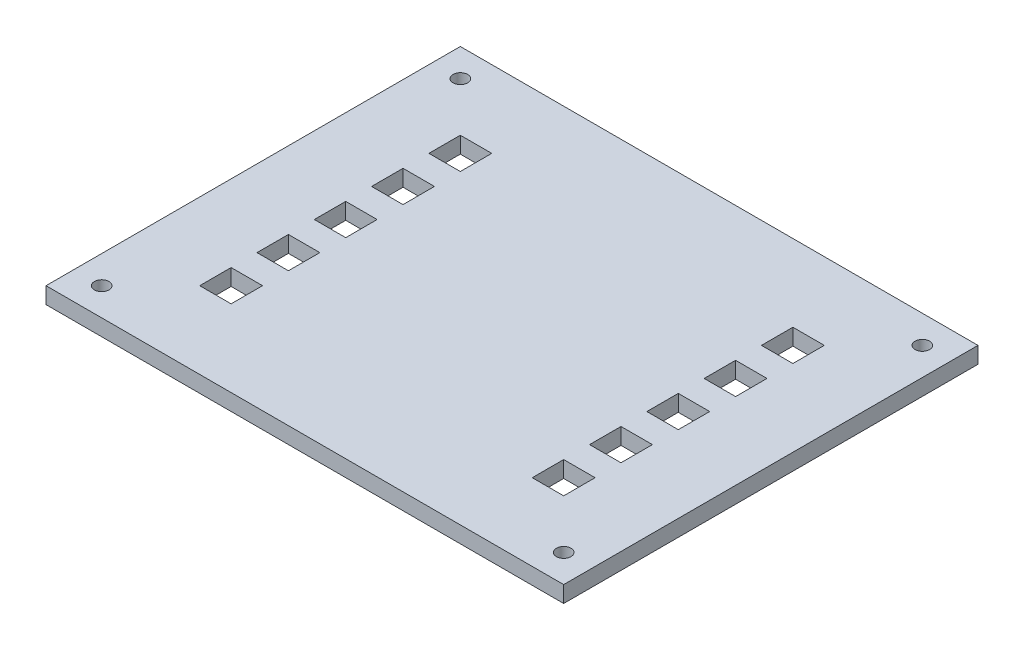
SolidWorks part; units mm, degrees
material "Maple"
ref_plane "Front Plane" through (0, 0, 0) normal (0, 0, 1) x (1, 0, 0)
ref_plane "Top Plane" through (0, 0, 0) normal (0, 1, 0) x (1, 0, 0)
ref_plane "Right Plane" through (0, 0, 0) normal (1, 0, 0) x (0, 0, -1)
sketch "Sketch1" plane through (0, 0, 0) normal (0, 1, 0) x (1, 0, 0)
  line L1 (-50.085, 40.085) -> (50.085, 40.085)
  line L2 (-50.085, 40.085) -> (-50.085, -40.085)
  line L3 (-50.085, -40.085) -> (50.085, -40.085)
  line L4 (50.085, 40.085) -> (50.085, -40.085)
  line L5 (-50.085, 40.085) -> (50.085, -40.085) construction
  line L6 (-50.085, -40.085) -> (50.085, 40.085) construction
  point P0 (0, 0)
  dimension "D1" = 100.17
  dimension "D2" = 80.17
extrude "Boss-Extrude1" add sketch "Sketch1" along normal blind 3.175
sketch "Sketch2" plane through (0, 3.175, 0) normal (0, 1, 0) x (1, 0, 0)
  line L0 (-35.3, 25.3) -> (35.3, 25.3) construction
  line L1 (-37.3, 27.3) -> (37.3, 27.3) construction
  line L2 (-37.3, 27.3) -> (-37.3, -27.3) construction
  line L3 (-37.3, -27.3) -> (37.3, -27.3) construction
  line L4 (37.3, 27.3) -> (37.3, -27.3) construction
  line L5 (-37.3, 27.3) -> (37.3, -27.3) construction
  line L6 (-37.3, -27.3) -> (37.3, 27.3) construction
  line L7 (35.3, 25.3) -> (35.3, -25.3) construction
  line L8 (-35.3, -25.3) -> (35.3, -25.3) construction
  line L9 (-35.3, 25.3) -> (-35.3, -25.3) construction
  line L10 (35.3, 19.05) -> (29.05, 19.05) construction
  line L19 (0, 0) -> (0, 10.7389) construction
  line L24 (-35.3, 25.3) -> (-29.05, 25.3) construction
  line L25 (-35.3, 25.3) -> (-35.3, 19.05) construction
  line L30 (-35.3, 19.05) -> (-29.05, 19.05) construction
  line L31 (-29.05, 25.3) -> (-29.05, 19.05) construction
  line L36 (29.05, 25.3) -> (29.05, 19.05) construction
  line L37 (35.3, 25.3) -> (29.05, 25.3) construction
  line L58 (35.3, 25.3) -> (35.3, 19.05) construction
  line L59 (-35.215, 25.215) -> (-35.215, 19.135)
  line L60 (-35.215, 19.135) -> (-29.135, 19.135)
  line L61 (-29.135, 25.215) -> (-29.135, 19.135)
  line L62 (-35.215, 25.215) -> (-29.135, 25.215)
  line L63 (35.215, 19.135) -> (29.135, 19.135)
  line L64 (29.135, 25.215) -> (29.135, 19.135)
  line L65 (35.215, 25.215) -> (29.135, 25.215)
  line L66 (35.215, 25.215) -> (35.215, 19.135)
  line L67 (-35.3, -25.215) -> (35.3, -25.215) construction
  point P0 (0, 0)
  dimension "D1" = 74.6
  dimension "D2" = 54.6
  dimension "D4" = 6.25
  dimension "D5" = 6.25
  dimension "D3" = 2
  dimension "D6" = 0.085
  dimension "D7" = 0.085
  dimension "D8" = 0.085
extrude "Cut-Extrude2" cut sketch "Sketch2" against normal through all
sketch "Sketch4" plane through (0, 3.175, 0) normal (0, 1, 0) x (1, 0, 0)
  line L0 (-44.6967, 34.6967) -> (-50, 40) construction
  line L2 (0, 0) -> (0, 17.6219) construction
  line L3 (0, 0) -> (14.8795, 0) construction
  line L22 (-50, 40) -> (-50, -40.085)
  line L23 (50.085, 40) -> (-50, 40)
  line L24 (-50, 40) -> (-50, -40.085) construction
  line L25 (50.085, 40) -> (-50, 40) construction
  circle A0 centre (-44.6967, 34.6967) radius 1.415
  circle A1 centre (44.6967, 34.6967) radius 1.415
  circle A2 centre (44.6967, -34.6967) radius 1.415
  circle A3 centre (-44.6967, -34.6967) radius 1.415
  dimension "D3" = 2.83
  dimension "D1" = 45
  dimension "D2" = 7.5
  dimension "D6" = 0.085
pattern_linear "LPattern1" count 5 spacing 11.0875 along (0, 0, 1) of "Cut-Extrude2"
extrude "Cut-Extrude3" cut sketch "Sketch4" against normal blind 6.35
equation "\"length\"=100"
equation "\"D1@Sketch1\"=\"length\" + 2*\"kerf\""
equation "\"width\"=80"
equation "\"D2@Sketch1\"=\"width\" + 2*\"kerf\""
equation "\"depth\"=6.35"
equation "\"depth2\"= 6.35 / 2"
equation "\"D1@Boss-Extrude1\"=\"depth2\""
equation "\"D1@Sketch2\"=\"length\" - 4*\"depth\""
equation "\"D2@Sketch2\"=\"width\" - 4*\"depth\""
equation "\"cut\"=6.25"
equation "\"D4@Sketch2\"=\"cut\""
equation "\"D5@Sketch2\"=\"cut\""
equation "\"kerf\"= 0.17 / 2"
